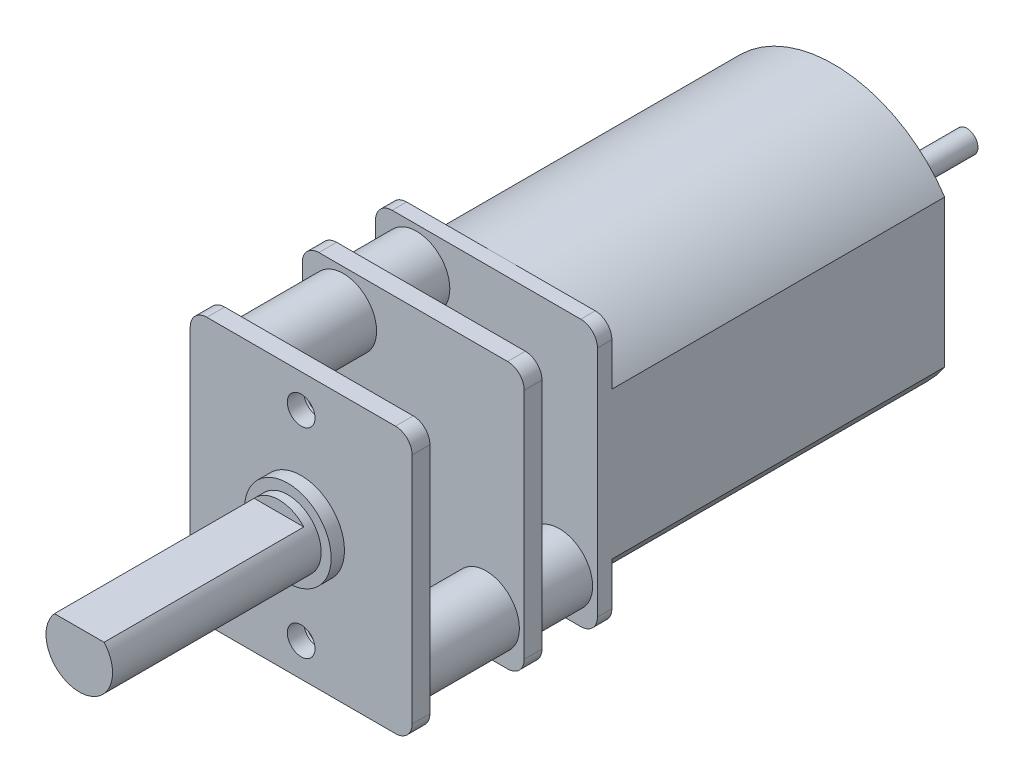
SolidWorks part; units mm, degrees
ref_plane "Front Plane" through (0, 0, 0) normal (0, 0, 1) x (1, 0, 0)
ref_plane "Top Plane" through (0, 0, 0) normal (0, 1, 0) x (1, 0, 0)
ref_plane "Right Plane" through (0, 0, 0) normal (1, 0, 0) x (0, 0, -1)
sketch "Sketch1" plane through (0, 0, 0) normal (0, 0, 1) x (1, 0, 0)
  line L1 (-5, -6) -> (5, -6)
  line L2 (-5, -6) -> (-5, 6)
  line L3 (-5, 6) -> (5, 6)
  line L4 (5, -6) -> (5, 6)
  line L5 (-5, -6) -> (5, 6) construction
  line L6 (-5, 6) -> (5, -6) construction
  point P0 (0, 0)
  dimension "D1" = 12
  dimension "D2" = 10
extrude "Boss-Extrude1" add sketch "Sketch1" against normal blind 9
sketch "Sketch2" plane through (0, 0, -9) normal (0, 0, -1) x (-1, 0, 0)
  line L0 (-5, 3.3166) -> (-5, -3.3166)
  line L1 (5, 3.3166) -> (5, -3.3166)
  line L2 (-5, 0) -> (5, 0) construction
  arc A0 (-5, -3.3166) -> (5, -3.3166) centre (0, 0) ccw
  arc A1 (5, 3.3166) -> (-5, 3.3166) centre (0, 0) ccw
  point P8 (0, 0)
  dimension "D2" = 6
  dimension "D1" = 10
extrude "Boss-Extrude2" add sketch "Sketch2" along normal blind 15
sketch "Sketch3" plane through (0, 0, 0) normal (1, 0, 0) x (0, 0, -1)
  line L0 (-10, 0) -> (30, 0)
  line L1 (30, 0) -> (30, 0.5)
  line L2 (30, 0.5) -> (24.5243, 0.5)
  line L3 (24.5243, 0.5) -> (24.5243, 0.7972)
  line L4 (24.5243, 0.7972) -> (25.5, 0.7972)
  line L5 (25.5, 0.7972) -> (25.5, 2.5)
  line L6 (25.5, 2.5) -> (0, 2.5)
  line L7 (0, 2.5) -> (0, 1.95)
  line L8 (0, 1.95) -> (-0.6, 1.95)
  line L9 (-0.6, 1.95) -> (-0.6, 1.5)
  line L10 (-0.6, 1.5) -> (-10, 1.5)
  line L11 (-10, 1.5) -> (-10, 0)
  line L12 (0, -6) -> (0, 6) construction
  line L13 (24, 3.3166) -> (24, -3.3166) construction
  dimension "D1" = 1.95
  dimension "D2" = 1.5
  dimension "D3" = 0.6
  dimension "D4" = 2.5
  dimension "D5" = 1.5
  dimension "D6" = 0.5
  dimension "D7" = 40
  dimension "D8" = 10
revolve "Revolve1" add sketch "Sketch3" angle 360 about L0
sketch "Sketch4" plane through (0, 0, 10) normal (0, 0, 1) x (1, 0, 0)
  line L0 (1.118, 1) -> (-1.118, 1)
  arc A0 (-1.118, 1) -> (1.118, 1) centre (0, 0) cw
  circle A1 centre (0, 0) radius 1.5 construction
  dimension "D1" = 1
extrude "Cut-Extrude1" cut sketch "Sketch4" against normal blind 9
fillet "Fillet1" radius 0.75 4 edges at (-5, -6, -4.5) (5, -6, -4.5) (5, 6, -4.5) (-5, 6, -4.5)
hole_wizard "M1.6x0.35 Tapped Hole1" positions "Sketch6" profile "Sketch5" tap size "M1.6x0.35" standard "ANSI Metric"
sketch "Sketch6" plane through (0, 0, 0) normal (0, 0, 1) x (1, 0, 0)
  line L0 (0, 4.5) -> (0, 0) construction
  line L1 (0, 0) -> (0, -4.5) construction
  point P0 (0, -4.5)
  point P2 (0, 4.5)
  dimension "D1" = 9
sketch "Sketch5" plane through (0, -4.5, 0) normal (1, 0, 0) x (0, -1, 0)
  line L0 (0, 0) -> (0, 1.1255)
  line L1 (0, 1.1255) -> (0.625, 0.75)
  line L2 (0.625, 0.75) -> (0.625, 0)
  line L5 (0.625, 0) -> (0, 0)
  line L10 (0, 1.1255) -> (-0.625, 0.75) construction
  line L11 (0, -6.35) -> (0, 107.95) construction
  dimension "Tap Drill Dia." = 1.25
  dimension "Tap Drill Depth" = 0.75
  dimension "Drill Angle" = 118
cosmetic thread "Hole Thread1" parameters "D1"=0.75, "D2"=1.6
cosmetic thread "Hole Thread2" parameters "D1"=0.75, "D2"=1.6
sketch "Sketch7" plane through (0, 0, 0) normal (0, 0, 1) x (1, 0, 0)
  line L0 (5, -5.25) -> (5, 5.25) construction
  line L1 (-5, 6) -> (5, 6)
  line L2 (-5, 6) -> (-5, -6)
  line L3 (-5, -6) -> (5, -6)
  line L4 (5, 6) -> (5, -6)
  line L5 (4.25, 6) -> (-4.25, 6) construction
  line L6 (-5, 5.25) -> (-5, -5.25) construction
  line L7 (-4.25, -6) -> (4.25, -6) construction
  circle A0 centre (-3.1519, 4.2321) radius 1.5
  circle A1 centre (3.2828, -4.1573) radius 1.5
  dimension "D1" = 3
extrude "Cut-Extrude2" cut sketch "Sketch7" against normal blind 4.25 from offset 0.8 offset against normal yes
sketch "Sketch8" plane through (0, 0, -5.05) normal (0, 0, 1) x (1, 0, 0)
  line L0 (5, -5.25) -> (5, 5.25) construction
  line L1 (-5, 6) -> (5, 6)
  line L2 (-5, 6) -> (-5, -6)
  line L3 (-5, -6) -> (5, -6)
  line L4 (5, 6) -> (5, -6)
  line L5 (-4.25, -6) -> (4.25, -6) construction
  line L6 (-5, 5.25) -> (-5, -5.25) construction
  line L7 (4.25, 6) -> (-4.25, 6) construction
  circle A0 centre (-3.1519, 4.2321) radius 1.5
  circle A1 centre (3.2828, -4.1573) radius 1.5
extrude "Cut-Extrude3" cut sketch "Sketch8" against normal blind 2.5 from offset 0.8
